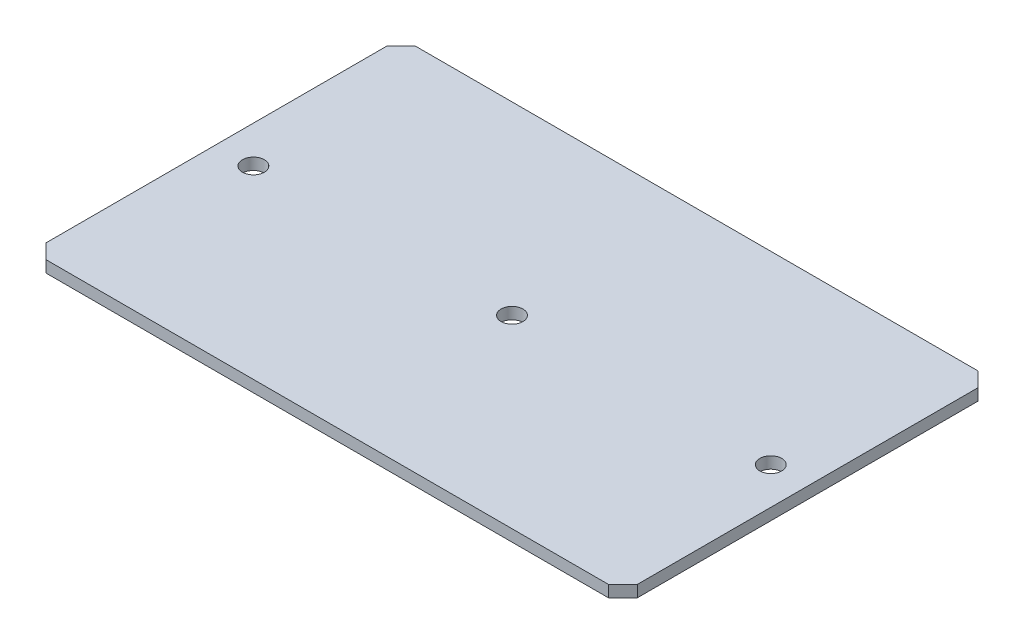
SolidWorks part; units mm, degrees
ref_plane "Front Plane" through (0, 0, 0) normal (0, 0, 1) x (1, 0, 0)
ref_plane "Top Plane" through (0, 0, 0) normal (0, 1, 0) x (1, 0, 0)
ref_plane "Right Plane" through (0, 0, 0) normal (1, 0, 0) x (0, 0, -1)
sketch "Sketch1" plane through (0, 0, 0) normal (0, 1, 0) x (1, 0, 0)
  line L1 (-40.64, 25.4) -> (40.64, 25.4)
  line L2 (-40.64, 25.4) -> (-40.64, -25.4)
  line L3 (-40.64, -25.4) -> (40.64, -25.4)
  line L4 (40.64, 25.4) -> (40.64, -25.4)
  line L5 (-40.64, 25.4) -> (40.64, -25.4) construction
  line L6 (-40.64, -25.4) -> (40.64, 25.4) construction
  point P0 (0, 0)
  dimension "D1" = 81.28
  dimension "D2" = 50.8
extrude "Boss-Extrude1" add sketch "Sketch1" along normal blind 1.6002
sketch "Sketch2" plane through (0, 1.6002, 0) normal (0, 1, 0) x (1, 0, 0)
  line L0 (-40.64, 0) -> (-35.54, 0) construction
  line L1 (-40.64, 25.4) -> (-40.64, -25.4) construction
  circle A0 centre (-35.54, 0) radius 1.5
  circle A2 centre (35.56, 0) radius 1.5
  circle A3 centre (0, 0) radius 1.5
  dimension "D1" = 71.1
  dimension "D3" = 3
  dimension "D4" = 3
  dimension "D5" = 3
  dimension "D2" = 5.1
  dimension "D6" = 35.56
extrude "Cut-Extrude1" cut sketch "Sketch2" against normal blind 1.6002
chamfer "Chamfer1" distance 2 angle 45 4 edges at (40.64, 0.8001, 25.4) (-40.64, 0.8001, 25.4) (-40.64, 0.8001, -25.4) (40.64, 0.8001, -25.4)
